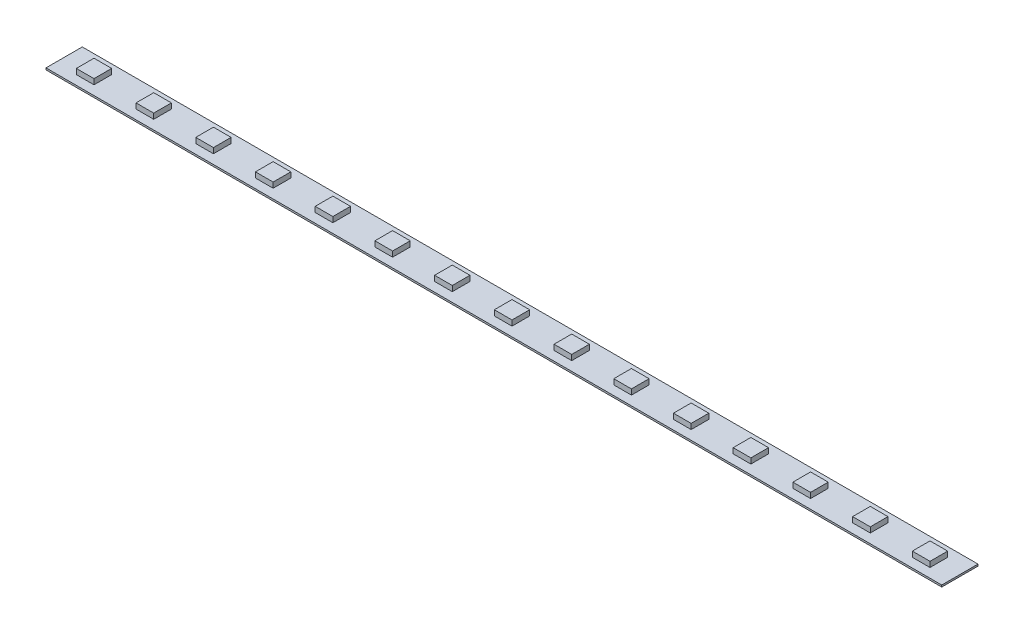
SolidWorks part; units mm, degrees
ref_plane "Front Plane" through (0, 0, 0) normal (0, 0, 1) x (1, 0, 0)
ref_plane "Top Plane" through (0, 0, 0) normal (0, 1, 0) x (1, 0, 0)
ref_plane "Right Plane" through (0, 0, 0) normal (1, 0, 0) x (0, 0, -1)
sketch "Sketch1" plane through (0, 0, 0) normal (0, 1, 0) x (1, 0, 0)
  line L1 (-2.46, -2.46) -> (2.46, -2.46)
  line L2 (-2.46, -2.46) -> (-2.46, 2.46)
  line L3 (-2.46, 2.46) -> (2.46, 2.46)
  line L4 (2.46, -2.46) -> (2.46, 2.46)
  line L5 (-2.46, -2.46) -> (2.46, 2.46) construction
  line L6 (-2.46, 2.46) -> (2.46, -2.46) construction
  point P0 (0, 0)
  dimension "D1" = 4.92
extrude "Boss-Extrude1" add sketch "Sketch1" along normal blind 2
pattern_linear "LPattern1" count 15 spacing 16.63 along (1, 0, 0) of "Boss-Extrude1"
sketch "Sketch2" plane through (0, 0, 0) normal (0, 1, 0) x (1, 0, 0)
  line L0 (0, 0) -> (267.2086, 0) construction
  line L1 (-8.315, 5.05) -> (241.135, 5.05)
  line L2 (-8.315, 5.05) -> (-8.315, -5.05)
  line L3 (-8.315, -5.05) -> (241.135, -5.05)
  line L4 (241.135, 5.05) -> (241.135, -5.05)
  dimension "D1" = 10.1
  dimension "D2" = 8.315
  dimension "D3" = 249.45
extrude "Boss-Extrude2" add sketch "Sketch2" along normal blind 0.5 contours L1 L4 L3 L2
ref_plane "Plane1" through (116.41, 0, 0) normal (-1, 0, 0) x (0, 0, 1)
equation "\"D2@Sketch2\"=16.63/2"
equation "\"D3@Sketch2\"=16.63*\"D1@LPattern1\""
